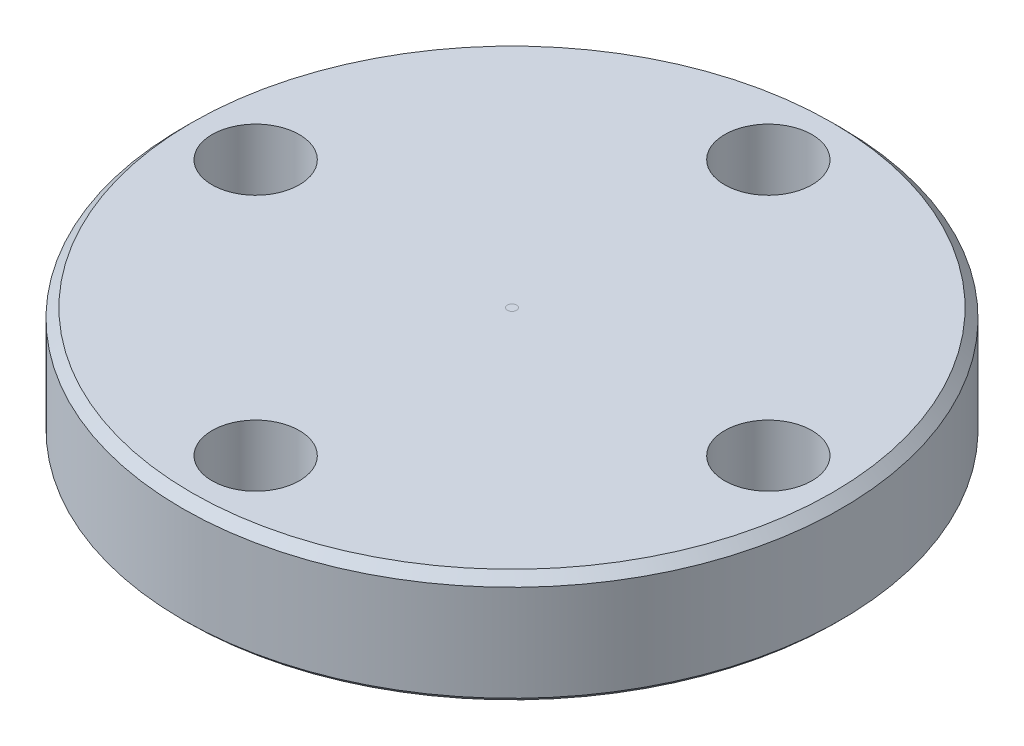
SolidWorks part; units mm, degrees
ref_plane "Front Plane" through (0, 0, 0) normal (0, 0, 1) x (1, 0, 0)
ref_plane "Top Plane" through (0, 0, 0) normal (0, 1, 0) x (1, 0, 0)
ref_plane "Right Plane" through (0, 0, 0) normal (1, 0, 0) x (0, 0, -1)
sketch "Sketch1" plane through (0, 0, 0) normal (0, 1, 0) x (1, 0, 0)
  circle A0 centre (0, 0) radius 36
  circle A1 centre (0, 0) radius 0.5
  dimension "D2" = 72
extrude "Boss-Extrude1" add sketch "Sketch1" along normal blind 12
sketch "Sketch4" plane through (0, 12, 0) normal (0, 1, 0) x (1, 0, 0)
  circle A0 centre (0, 0) radius 28
  circle A1 centre (0, -28) radius 4.765
  dimension "D1" = 56
  dimension "D2" = 9.53
extrude "Cut-Extrude1" cut sketch "Sketch4" against normal blind 12 contours A1
pattern_circular "CirPattern1" count 4 over 360 about axis through (0, 0, 0) along (0, 1, 0) of "Cut-Extrude1"
chamfer "Chamfer1" distance 1 angle 45 1 edges at (0, 12, 36)
chamfer "Chamfer2" distance 0.5 angle 45 1 edges at (0, 0, 36)
sketch "Sketch5" plane through (0, 0, 0) normal (0, 1, 0) x (1, 0, 0)
  circle A0 centre (0, 0) radius 0.4997
extrude "Boss-Extrude2" add sketch "Sketch5" along normal through all separate body
